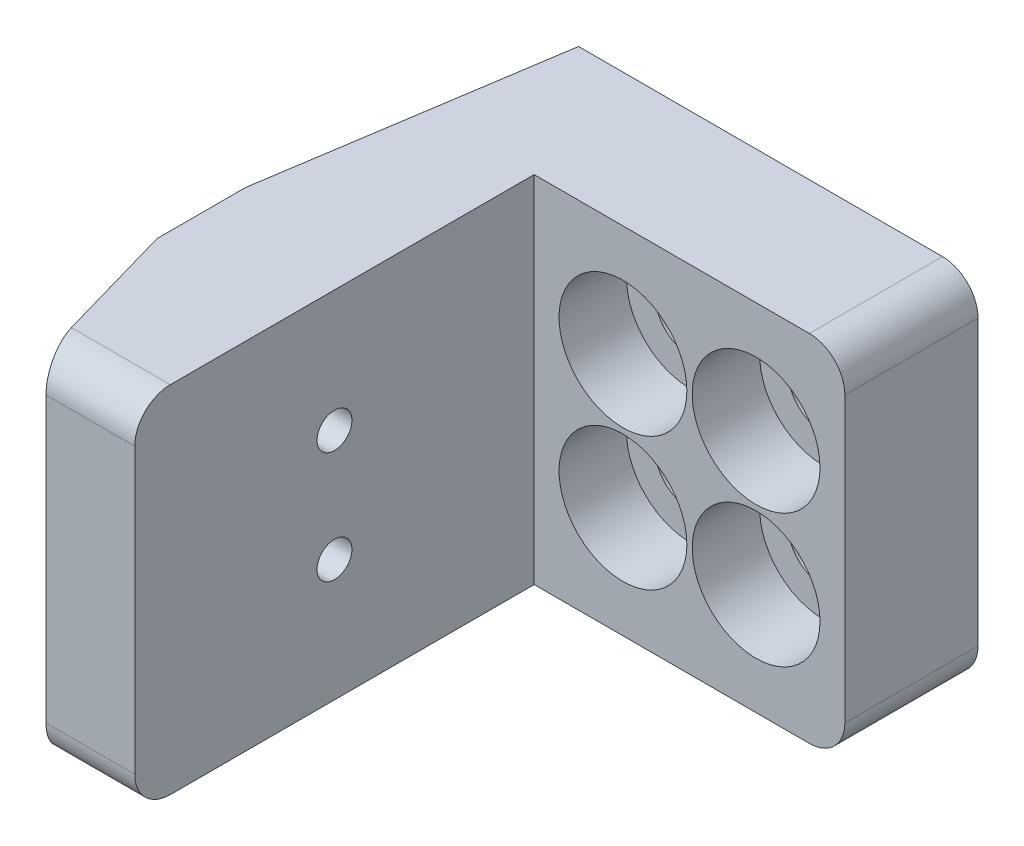
SolidWorks part; units mm, degrees
material "PET"
ref_plane "Front" through (0, 0, 0) normal (0, 0, 1) x (1, 0, 0)
ref_plane "Top" through (0, 0, 0) normal (0, 1, 0) x (1, 0, 0)
ref_plane "Right" through (0, 0, 0) normal (1, 0, 0) x (0, 0, -1)
sketch "Sketch1" plane through (0, 0, 0) normal (0, 1, 0) x (1, 0, 0)
  line L0 (0, 0) -> (22.225, 0)
  line L1 (22.225, 0) -> (22.225, 9.525)
  line L2 (22.225, 9.525) -> (-6.35, 9.525)
  line L4 (-6.35, -28.575) -> (0, -28.575)
  line L5 (0, -28.575) -> (0, 0)
  line L6 (-9.525, -11.1125) -> (-9.525, -17.4625)
  line L7 (-9.525, -17.4625) -> (-6.35, -28.575)
  line L8 (-9.525, -11.1125) -> (-6.35, 9.525)
  line L9 (-9.525, -14.2875) -> (0, -14.2875) construction
  dimension "D1" = 9.525
  dimension "D2" = 22.225
  dimension "D3" = 9.525
  dimension "D4" = 28.575
  dimension "D5" = 6.35
  dimension "D6" = 6.35
extrude "Boss-Extrude1" add sketch "Sketch1" along normal blind 25.4
sketch "Sketch4" plane through (0, 0, 0) normal (0, 0, 1) x (1, 0, 0)
  line L0 (0, 25.4) -> (6.35, 17.4625) construction
  line L2 (15.875, 7.9375) -> (22.225, 0) construction
  point P0 (6.35, 17.4625)
  point P2 (15.875, 7.9375)
  point P21 (6.35, 7.9375)
  point P23 (15.875, 17.4625)
  point P25 (0, 0)
  point P26 (0, 25.4)
  point P28 (14.399, 6.7567)
  dimension "D1" = 9.525
  dimension "D2" = 9.525
hole_wizard "CBORE for #10 Socket Head Cap Screw1" positions "Sketch4" profile "Sketch5" counterbore size "#10" standard "ANSI Inch" end condition through all
sketch "Sketch5" plane through (6.35, 17.4625, 0) normal (1, 0, 0) x (0, -1, 0)
  line L0 (0, 0) -> (0, 9.525)
  line L1 (0, 9.525) -> (2.5527, 9.525)
  line L3 (2.5527, 9.525) -> (2.5527, 4.826)
  line L4 (2.5527, 4.826) -> (4.572, 4.826)
  line L5 (4.572, 4.826) -> (4.572, 0)
  line L7 (4.572, 0) -> (0, 0)
  line L11 (0, -6.35) -> (0, 107.95) construction
  dimension "Thru Hole Dia." = 5.1054
  dimension "Thru Hole Depth" = 9.525
  dimension "C'Bore Dia." = 9.144
  dimension "C'Bore Depth" = 4.826
sketch "Sketch8" plane through (0, 0, 0) normal (1, 0, 0) x (0, 0, -1)
  line L2 (-14.2875, 8.7) -> (0, 0) construction
  line L3 (-28.575, 25.4) -> (-14.2875, 16.7) construction
  point P0 (-14.2875, 16.7)
  point P2 (-14.2875, 8.7)
  dimension "D1" = 8
hole_wizard "M3x0.5 Tapped Hole1" positions "Sketch8" profile "Sketch7" tap size "M3x0.5" standard "ANSI Metric" end condition through all
sketch "Sketch7" plane through (0, 16.7, 14.2875) normal (0, 1, 0) x (0, 0, -1)
  line L0 (0, 0) -> (0, 9.525)
  line L1 (0, 9.525) -> (1.25, 9.525)
  line L2 (1.25, 9.525) -> (1.25, 0)
  line L5 (1.25, 0) -> (0, 0)
  line L11 (0, -6.35) -> (0, 107.95) construction
  dimension "Thru Tap Drill Dia." = 2.5
  dimension "Thru Tap Drill Depth" = 9.525
cosmetic thread "Hole Thread1" parameters "D2"=3
cosmetic thread "Hole Thread2" parameters "D2"=3
fillet "Fillet1" radius 2.54 4 edges at (-3.175, 0, 28.575) (-3.175, 25.4, 28.575) (22.225, 0, -4.7625) (22.225, 25.4, -4.7625)
